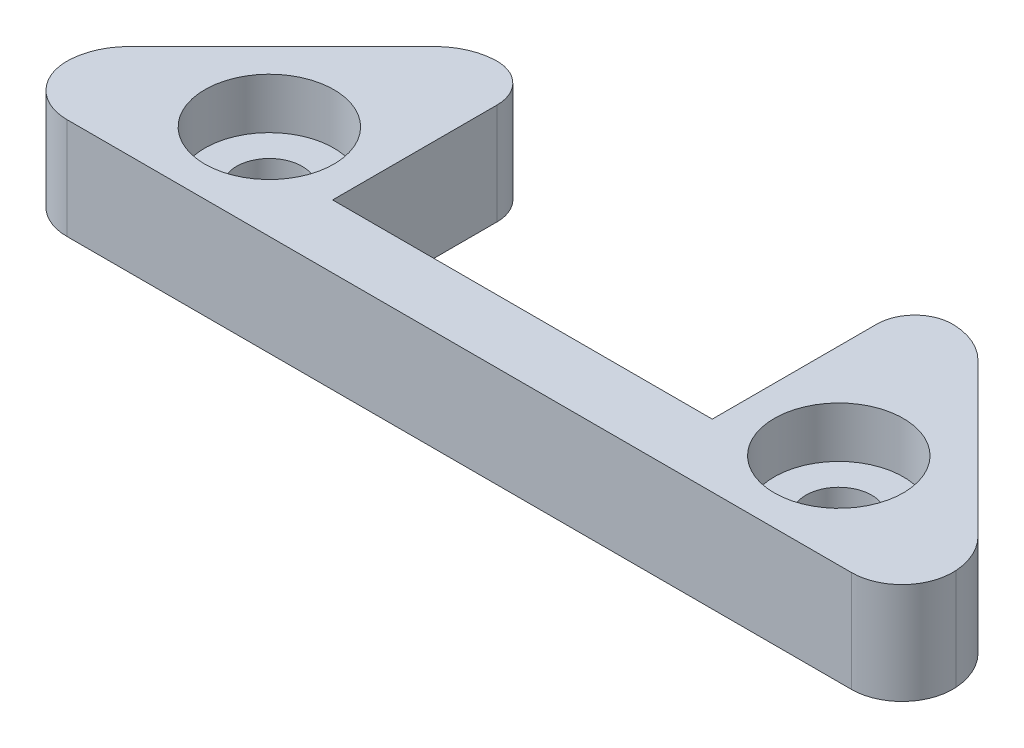
SolidWorks part; units mm, degrees
ref_plane "Plan de face" through (0, 0, 0) normal (0, 0, 1) x (1, 0, 0)
ref_plane "Plan de dessus" through (0, 0, 0) normal (0, 1, 0) x (1, 0, 0)
ref_plane "Plan de droite" through (0, 0, 0) normal (1, 0, 0) x (0, 0, -1)
sketch "Esquisse1" plane through (0, 0, 0) normal (0, 1, 0) x (1, 0, 0)
  line L0 (30, 0) -> (15, 15) construction
  line L1 (15, 0) -> (30, 0) construction
  line L2 (15, 15) -> (30, 15) construction
  line L3 (30, 0) -> (30, 15) construction
  line L4 (-15, 0) -> (-30, 0) construction
  line L5 (-15, 0) -> (-15, 15) construction
  line L6 (-15, 15) -> (-30, 15) construction
  line L7 (-30, 0) -> (-30, 15) construction
  line L8 (-15, 15) -> (-30, 0) construction
  line L9 (-15, 0) -> (15, 0) construction
  line L10 (-35, 0) -> (35, 0)
  line L13 (-15, 0) -> (-15, 5) construction
  line L16 (15, 0) -> (15, 5) construction
  line L17 (15, 15) -> (15, 5) construction
  line L18 (15, 5) -> (15, 21)
  line L21 (-15, 21) -> (-15, 5)
  line L22 (-15, 5) -> (15, 5)
  line L23 (-35, 0) -> (-35, 6)
  line L24 (-35, 6) -> (-20, 21)
  line L25 (-20, 21) -> (-15, 21)
  line L26 (15, 21) -> (20, 21)
  line L27 (20, 21) -> (35, 6)
  line L28 (35, 6) -> (35, 0)
  circle A0 centre (22.5, 7.5) radius 2.6
  circle A1 centre (-22.5, 7.5) radius 2.6
  circle A2 centre (22.5, 7.5) radius 7.5 construction
  point P17 (0, 0)
  point P24 (0, 0)
  dimension "D1" = 5.2
  dimension "D2" = 30
  dimension "D3" = 15
  dimension "D4" = 5
  dimension "D5" = 16
  dimension "D6" = 5
  dimension "D7" = 6
  dimension "D8" = 20
extrude "Boss.-Extru.1" add sketch "Esquisse1" along normal blind 8
sketch "Esquisse3" plane through (0, 8, 0) normal (0, 1, 0) x (1, 0, 0)
  circle A0 centre (-22.5, 7.5) radius 5.1
  circle A1 centre (22.5, 7.5) radius 5.1
  point P7 (22.5, 7.5)
  dimension "D1" = 10.2
extrude "Enlèv. mat.-Extru.2" cut sketch "Esquisse3" against normal blind 4
sketch "Esquisse4" plane through (0, 0, 0) normal (0, -1, 0) x (1, 0, 0)
  circle A0 centre (-22.5, -7.5) radius 4.5
  circle A1 centre (-22.5, -7.5) radius 5.5
  circle A2 centre (22.5, -7.5) radius 5.5
  circle A3 centre (22.5, -7.5) radius 4.5
  dimension "D1" = 9
  dimension "D2" = 11
extrude "Enlèv. mat.-Extru.3" cut sketch "Esquisse4" against normal blind 2
fillet "Congé1" radius 5 4 edges at (-35, 4, -6) (-20, 4, -21) (35, 4, -6) (20, 4, -21)
fillet "Congé2" radius 3 2 edges at (-15, 4, -21) (15, 4, -21)
fillet "Congé3" radius 4 2 edges at (-35, 4, 0) (35, 4, 0)
